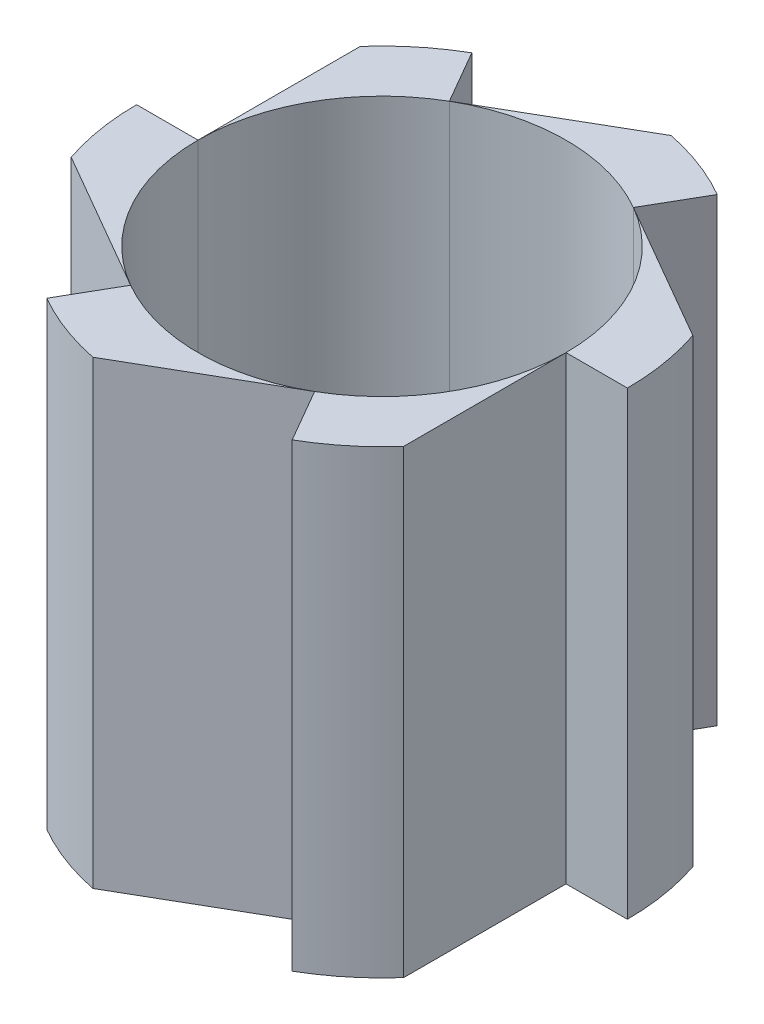
SolidWorks part; units mm, degrees
ref_plane "Front Plane" through (0, 0, 0) normal (0, 0, 1) x (1, 0, 0)
ref_plane "Top Plane" through (0, 0, 0) normal (0, 1, 0) x (1, 0, 0)
ref_plane "Right Plane" through (0, 0, 0) normal (1, 0, 0) x (0, 0, -1)
sketch "Sketch1" plane through (0, 0, 0) normal (0, 1, 0) x (1, 0, 0)
  line L3 (18, 0) -> (24, 0)
  line L4 (9, 15.5885) -> (12, 20.7846)
  line L5 (-9, 15.5885) -> (-12, 20.7846)
  line L6 (-18, 0) -> (-24, 0)
  line L7 (-9, -15.5885) -> (-12, -20.7846)
  line L8 (9, -15.5885) -> (12, -20.7846)
  line L9 (9, 15.5885) -> (22.7477, 7.6512)
  line L10 (18, 0) -> (18, -15.8745)
  line L11 (9, -15.5885) -> (-4.7477, -23.5257)
  line L12 (-9, -15.5885) -> (-22.7477, -7.6512)
  line L13 (-18, 0) -> (-18, 15.8745)
  line L14 (-9, 15.5885) -> (4.7477, 23.5257)
  circle A0 centre (0, 0) radius 18
  circle A1 centre (0, 0) radius 25 construction
  arc A2 (-24, 0) -> (-22.7477, -7.6512) centre (0, 0) ccw
  arc A3 (-12, -20.7846) -> (-4.7477, -23.5257) centre (0, 0) ccw
  arc A4 (12, -20.7846) -> (18, -15.8745) centre (0, 0) ccw
  arc A5 (24, 0) -> (22.7477, 7.6512) centre (0, 0) ccw
  arc A6 (12, 20.7846) -> (4.7477, 23.5257) centre (0, 0) ccw
  arc A7 (-12, 20.7846) -> (-18, 15.8745) centre (0, 0) ccw
  point P8 (0, 0)
  point P10 (0, 0)
  dimension "D2" = 50
  dimension "D3" = 48
extrude "Boss-Extrude1" add sketch "Sketch1" along normal blind 45 contours L7 A3 L11 A0 | L8 A4 L10 A0 | L3 A5 L9 A0 | L4 A6 L14 A0 | L5 A7 L13 A0 | L6 A2 L12 A0
